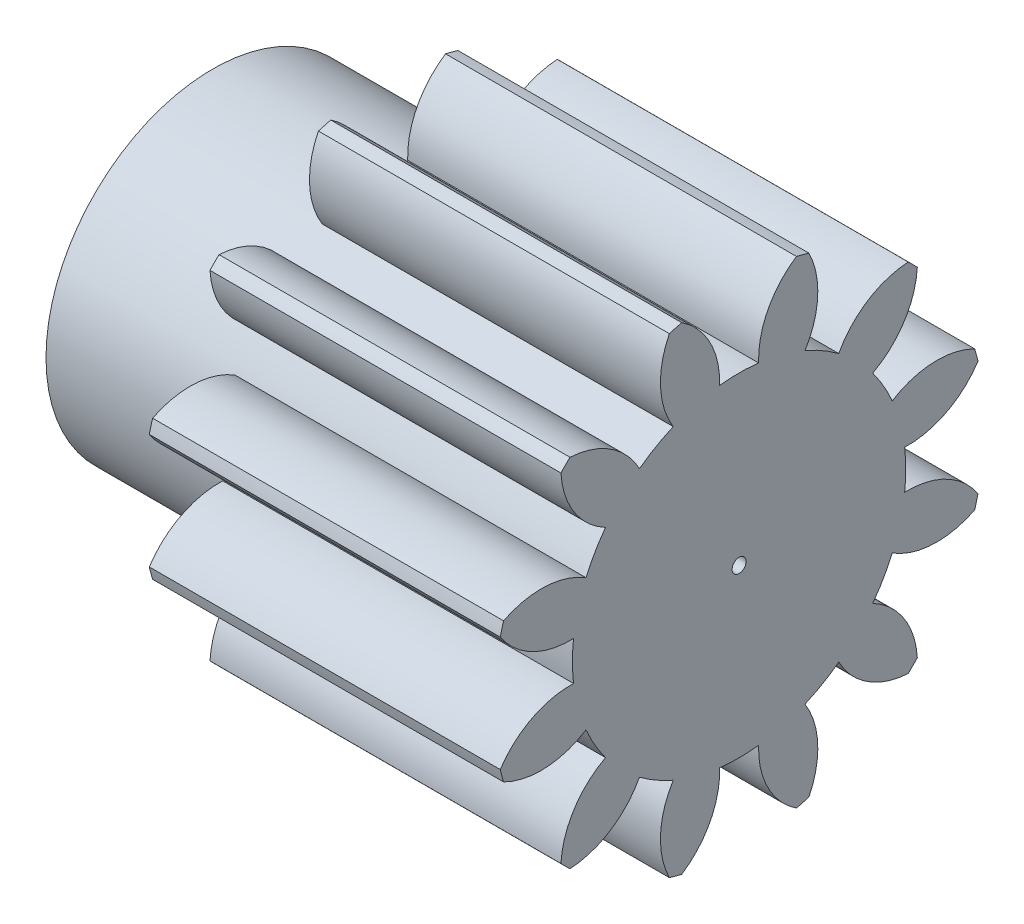
SolidWorks part; units mm, degrees
ref_plane "Plane1" through (0, 0, 0) normal (0, 0, 1) x (1, 0, 0)
ref_plane "Plane2" through (0, 0, 0) normal (0, 1, 0) x (1, 0, 0)
ref_plane "Plane3" through (0, 0, 0) normal (1, 0, 0) x (0, 0, -1)
sketch "HoldingSke" plane through (0, 0, 0) normal (0, 1, 0) x (1, 0, 0)
  line L0 (0, 0) -> (0.4891, -0.104)
  line L1 (-15, 0) -> (100, 0) construction
  line L2 (0, 0) -> (-2.1039, 2.3779)
  line L3 (0, 0) -> (-11.863, 4.5341)
  line L4 (0, 0) -> (8.4473, 1.7955)
  line L5 (0, 0) -> (-28.1086, -10.4837)
  line L6 (0, 0) -> (-16.5793, -11.1861)
  line L7 (-2.1039, 2.3779) -> (4.3536, 31.6747)
  line L8 (-76.2, 54.61) -> (-76.1, 54.61)
  line L9 (-71.009, 38.7566) -> (-53.1078, 45.2721)
  line L10 (-76.2, 71.12) -> (104.1128, 71.12)
  line L11 (0, 0) -> (-20, 0)
  line L12 (-76.2, 101.6) -> (-76.133, 101.6)
  line L13 (24.9733, 27.94) -> (52.9518, 28.4284)
  line L14 (24.9733, 27.94) -> (24.9743, 27.94)
  line L15 (24.9733, 27.94) -> (100.4006, 29.5858)
  line L16 (-63.627, -2) -> (-12.827, -2)
  circle A0 centre (0, 0) radius 0.4
  circle A1 centre (0, 0) radius 9.499
  circle A2 centre (0, 0) radius 9.5
  circle A3 centre (0, 0) radius 0.4
  dimension "MHD" = 18.998
  dimension "Hub_dia" = 19
  dimension "Bore" = 0.8
  dimension "MBD" = 0.8
  dimension "Num_teeth" = 12
  dimension "Pitch" = 0.5
  dimension "Overall_len" = 30
  dimension "Show_teeth" = 12
  dimension "Thickness" = 20
  dimension "OAL" = 30.0001
  dimension "T_dim" = 0.1
  dimension "Ap" = 20
  dimension "H" = 19.05
  dimension "Pitch_radius" = 180.3128
  dimension "Width" = 20
  dimension "Backlash" = 0.067
  dimension "Addendum_fac" = 1
  dimension "Dedendum_fac" = 1.25
  dimension "Clearance_fac" = 0.25
  dimension "Dedendum_add" = 0.001
  dimension "Module" = 2
sketch "BasProSke" plane through (0, 0, 0) normal (0, 1, 0) x (1, 0, 0)
  line L0 (-10, 0) -> (60, 0) construction
  line L1 (0, 0) -> (0, 14)
  line L2 (0, 0) -> (20, 0)
  line L3 (20, 0) -> (20, 14)
  line L4 (20, 14) -> (0, 14)
  dimension "Thickness" = 20
  dimension "Diameter" = 28
revolve "Base-Revolve" add sketch "BasProSke" angle 360 about L0
sketch "TooCutSke" plane through (0, 0, 0) normal (1, 0, 0) x (0, 0, -1)
  line L1 (0, 0) -> (0, 107) construction
  line L2 (0, 0) -> (-1.6834, 11.8813) construction
  line L3 (0, 0) -> (-6.1662, 23.0126) construction
  line L4 (-1.6834, 11.8813) -> (-3.0831, 11.5063) construction
  arc A0 (1.1119, 9.4337) -> (-1.1119, 9.4337) centre (0, 0) ccw
  arc A1 (3.2981, 13.6321) -> (-3.2981, 13.6321) centre (0, 0) ccw
  circle A2 centre (0, 0) radius 12 construction
  circle A3 centre (0, 0) radius 11.2763 construction
  arc A4 (-1.1119, 9.4337) -> (-3.2981, 13.6321) centre (-5.9089, 9.6042) ccw
  arc A5 (3.2981, 13.6321) -> (1.1119, 9.4337) centre (5.9089, 9.6042) ccw
  dimension "Root_dia" = 18.998
  dimension "Overcut_dia" = 28.0508
  dimension "Pitch_dia" = 24
  dimension "Base_dia" = 22.5526
  dimension "Flank_rad" = 4.8
  dimension "Half_ang" = 15
  dimension "Half_CT" = 1.4491
extrude "ToothCut" cut sketch "TooCutSke" along normal through all
fillet "Breaks" [suppressed] radius 0.04
fillet "RootFillets" [suppressed] radius 0.501
pattern_circular "TeethCuts" count 12 every 30 about axis through (-10, 0, 0) along (1, 0, 0) of "ToothCut", "RootFillets", "Breaks"
sketch "HubNeaOneSke" plane through (0, 0, 0) normal (-1, 0, 0) x (0, 0, 1)
  circle A0 centre (0, 0) radius 9.499
  dimension "Diameter" = 18.998
extrude "HubNearOne" add sketch "HubNeaOneSke" along normal blind 10.0001
sketch "HubNeaBotSke" plane through (0, 0, 0) normal (-1, 0, 0) x (0, 0, 1)
  circle A0 centre (0, 0) radius 9.499
  dimension "Diameter" = 18.998
extrude "HubNearBoth" [suppressed] add sketch "HubNeaBotSke" along normal blind 5
ref_plane "FarPln" through (20, 0, 0) normal (1, 0, 0) x (0, 0, -1)
sketch "HubFarSke" plane through (20, 0, 0) normal (1, 0, 0) x (0, 0, -1)
  circle A0 centre (0, 0) radius 9.499
  dimension "Diameter" = 18.998
extrude "HubFar" [suppressed] add sketch "HubFarSke" along normal blind 5
sketch "BorSke" plane through (0, 0, 0) normal (1, 0, 0) x (0, 0, -1)
  circle A0 centre (0, 0) radius 0.4
  dimension "Diameter" = 0.8
extrude "Bore" cut sketch "BorSke" along normal mid plane 60.0001
sketch "KeySke" plane through (0, 0, 0) normal (1, 0, 0) x (0, 0, -1)
  line L0 (-0.05, 0) -> (-0.05, 0.5)
  line L1 (-0.05, 0.5) -> (0.05, 0.5)
  line L2 (0.05, 0.5) -> (0.05, 0)
  line L3 (0, 0) -> (0, 34) construction
  line L4 (-0.05, 0) -> (0.05, 0)
  dimension "Offset" = 0.5
  dimension "Width" = 0.1
extrude "Keyway" [suppressed] cut sketch "KeySke" along normal mid plane 60.0001
pattern_circular "Keyway2" [suppressed] count 2 every 90 about axis through (-10, 0, 0) along (1, 0, 0)
equation "' \"Module@HoldingSke\" = 6.35"
equation "' \"Num_teeth@HoldingSke\" = 12"
equation "' \"Ap@HoldingSke\" =  20"
equation "' \"Ap@HoldingSke\" = 20"
equation "' \"Width@HoldingSke\" = 0.5 * 25.4"
equation "' \"Hub_dia@HoldingSke\"= 1 * 25.4"
equation "' \"Hub_dia@HoldingSke\" = 1 * 25.4"
equation "' \"Overall_len@HoldingSke\" = 1.0 * 25.4"
equation "' \"Bore@HoldingSke\" = 0.75 * 25.4"
equation "' \"T_dim@HoldingSke\" = 0.1 * 25.4"
equation "' \"Width@KeySke\" = 0.25 * 25.4"
equation "' \"Show_teeth@HoldingSke\" = 13"
equation "' \"Backlash@HoldingSke\" = 0.009 * 25.4"
equation "' \"Addendum_fac@HoldingSke\" = 1.0"
equation "' \"Dedendum_fac@HoldingSke\" = 1.25"
equation "' \"Dedendum_add@HoldingSke\" = 0.00005 * 25.4"
equation "' \"Clearance_fac@HoldingSke\" = 0.25"
equation "\"Pitch@HoldingSke\" = 1 / \"Module@HoldingSke\""
equation "\"Overcut_dia@TooCutSke\" = (\"Num_teeth@HoldingSke\" + 2 * \"Addendum_fac@HoldingSke\") / \"Pitch@HoldingSke\" + 0.002 * 25.4"
equation "\"Pitch_dia@TooCutSke\" = \"Num_teeth@HoldingSke\" / \"Pitch@HoldingSke\""
equation "\"Base_dia@TooCutSke\" = \"Num_teeth@HoldingSke\" / \"Pitch@HoldingSke\" * cos((\"Ap@HoldingSke\"  * 3.14159265 / 180))"
equation "\"Root_dia@TooCutSke\" = (\"Num_teeth@HoldingSke\" + 2) / \"Pitch@HoldingSke\" - 2 * (\"Addendum_fac@HoldingSke\" + \"Dedendum_fac@HoldingSke\") / \"Pitch@HoldingSke\" - \"Dedendum_add@HoldingSke\" * 2"
equation "\"Half_ang@TooCutSke\" = 180 / \"Num_teeth@HoldingSke\""
equation "\"Half_CT@TooCutSke\" = \"Num_teeth@HoldingSke\" / \"Pitch@HoldingSke\" * sin((3.14159265 / 2 / \"Num_teeth@HoldingSke\")) / 2 - 7 * \"Backlash@HoldingSke\" / 4"
equation "\"Flank_rad@TooCutSke\" = \"Num_teeth@HoldingSke\" / \"Pitch@HoldingSke\" / 5"
equation "\"Radius@RootFillets\" = \"Clearance_fac@HoldingSke\" / \"Pitch@HoldingSke\" + \"Dedendum_add@HoldingSke\""
equation "\"Break_rad@Breaks\" = 0.02 / \"Pitch@HoldingSke\""
equation "\"Thickness@HoldingSke\" = \"Width@HoldingSke\""
equation "\"OAL@HoldingSke\" = \"Thickness@HoldingSke\""
equation "\"MHD@HoldingSke\" = (\"Num_teeth@HoldingSke\" + 2) / \"Pitch@HoldingSke\" - 2 * (\"Addendum_fac@HoldingSke\" + \"Dedendum_fac@HoldingSke\")  / \"Pitch@HoldingSke\" - \"Dedendum_add@HoldingSke\" * 2"
equation "\"MBD@HoldingSke\" = (\"Num_teeth@HoldingSke\" + 2) / \"Pitch@HoldingSke\" - 2 * (\"Addendum_fac@HoldingSke\" + \"Dedendum_fac@HoldingSke\")  / \"Pitch@HoldingSke\" - \"Dedendum_add@HoldingSke\" * 2 - 0.002 * 25.4"
equation "\"MHD@HoldingSke\" = ((sgn( \"MHD@HoldingSke\" - \"Hub_dia@HoldingSke\" )-1)*( \"MHD@HoldingSke\" - \"Hub_dia@HoldingSke\" ))/-2+ \"Hub_dia@HoldingSke\""
equation "\"MBD@HoldingSke\" = ((sgn( \"MBD@HoldingSke\" - \"Bore@HoldingSke\" )-1)*( \"MBD@HoldingSke\" - \"Bore@HoldingSke\" ))/-2+ \"Bore@HoldingSke\""
equation "\"OAL@HoldingSke\" = ((sgn( \"OAL@HoldingSke\" - \"Overall_len@HoldingSke\" )+1)*( \"OAL@HoldingSke\" - \"Overall_len@HoldingSke\" ))/2 + \"Overall_len@HoldingSke\" + 0.000002 * 25.4"
equation "\"Num_teeth@TeethCuts\" = int( \"Show_teeth@HoldingSke\" ) + 1"
equation "\"Num_teeth@TeethCuts\" = ((sgn( \"Num_teeth@TeethCuts\" - \"Num_teeth@HoldingSke\" )-1)*( \"Num_teeth@TeethCuts\" - \"Num_teeth@HoldingSke\" ))/-2+ \"Num_teeth@HoldingSke\""
equation "\"Num_teeth@TeethCuts\" = ((sgn( \"Num_teeth@TeethCuts\" - 2.0)+1)*( \"Num_teeth@TeethCuts\" - 2.0))/2 +2.0"
equation "\"Angle@TeethCuts\" = 360.0 / \"Num_teeth@HoldingSke\""
equation "\"Diameter@BasProSke\" = (\"Num_teeth@HoldingSke\" + 2 * \"Addendum_fac@HoldingSke\") / \"Pitch@HoldingSke\""
equation "\"Thickness@BasProSke\"  = \"Thickness@HoldingSke\""
equation "' \"Fillet_rad@BasProSke\" =  \"Thickness@HoldingSke\" * 0.05"
equation "' \"Fillet_rad@BasProSke\" = \"Thickness@HoldingSke\" * 0.05"
equation "\"MHD@HoldingSke\" = ((sgn( \"MHD@HoldingSke\" - \"Root_dia@TooCutSke\" )-1)*( \"MHD@HoldingSke\" - \"Root_dia@TooCutSke\" ))/-2+ \"Root_dia@TooCutSke\""
equation "\"Diameter@HubNeaOneSke\" = \"MHD@HoldingSke\""
equation "\"Length@HubNearOne\" = \"OAL@HoldingSke\" - \"Thickness@BasProSke\""
equation "\"Diameter@HubNeaBotSke\" = \"MHD@HoldingSke\""
equation "\"Length@HubNearBoth\" = ( \"OAL@HoldingSke\" - \"Thickness@BasProSke\" ) / 2.0"
equation "\"Thickness@FarPln\" = \"Thickness@BasProSke\""
equation "\"Diameter@HubFarSke\" = \"MHD@HoldingSke\""
equation "\"Length@HubFar\" = ( \"OAL@HoldingSke\" - \"Thickness@BasProSke\" ) / 2.0"
equation "\"Diameter@BorSke\" = \"MBD@HoldingSke\""
equation "\"D1@Bore\" = \"OAL@HoldingSke\" * 2.0"
equation "\"D1@Keyway\" = \"OAL@HoldingSke\" * 2.0"
equation "\"Offset@KeySke\" = \"T_dim@HoldingSke\" + \"MBD@HoldingSke\" / 2.0"
